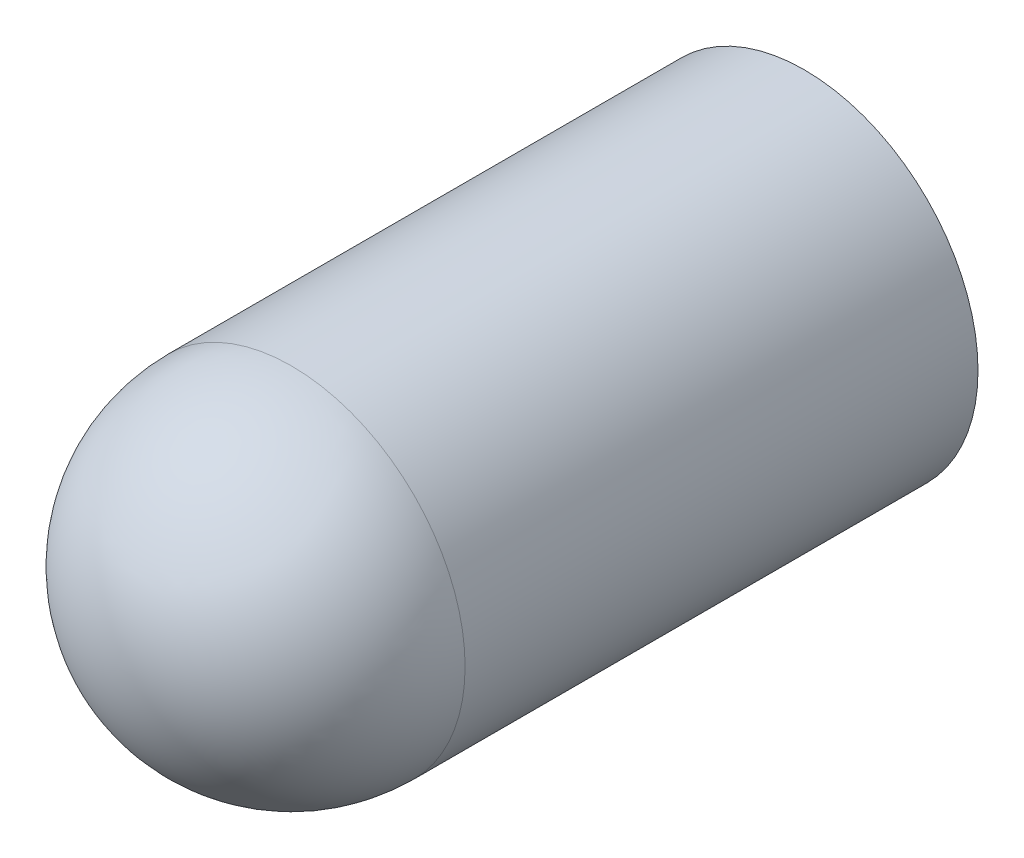
SolidWorks part; units mm, degrees
material "PP Homopolymer"
ref_plane "X-Y Datum" through (0, 0, 0) normal (0, 0, 1) x (1, 0, 0)
ref_plane "X-Z Datum" through (0, 0, 0) normal (0, 1, 0) x (1, 0, 0)
ref_plane "Y-Z Datum" through (0, 0, 0) normal (1, 0, 0) x (0, 0, -1)
sketch "Sketch1" plane through (0, 0, 0) normal (0, 1, 0) x (1, 0, 0)
  line L8 (1.27, 0) -> (-1.27, 0) construction
  line L9 (1.27, 0) -> (1.27, -8.255)
  line L10 (-1.27, 0) -> (-1.27, -8.255) construction
  line L11 (1.27, 0) -> (2.794, 0)
  line L12 (2.794, 0) -> (2.794, -8.255)
  line L13 (-1.27, 0) -> (-2.794, 0) construction
  line L14 (-2.794, 0) -> (-2.794, -8.255) construction
  line L15 (0, 0) -> (0, -11.049) construction
  line L16 (0, -11.049) -> (0, -9.525)
  arc A0 (-1.27, -8.255) -> (1.27, -8.255) centre (0, -8.255) ccw construction
  arc A1 (-2.794, -8.255) -> (2.794, -8.255) centre (0, -8.255) ccw construction
  arc A2 (1.27, -8.255) -> (0, -9.525) centre (0, -8.255) cw
  arc A3 (2.794, -8.255) -> (0, -11.049) centre (0, -8.255) cw
  point P3 (0, 0)
  point P6 (0, -9.525)
  dimension "D2" = 9.525
  dimension "D1" = 2.54
  dimension "D3" = 1.524
revolve "Revolve2" add sketch "Sketch1" angle 360 about L15
